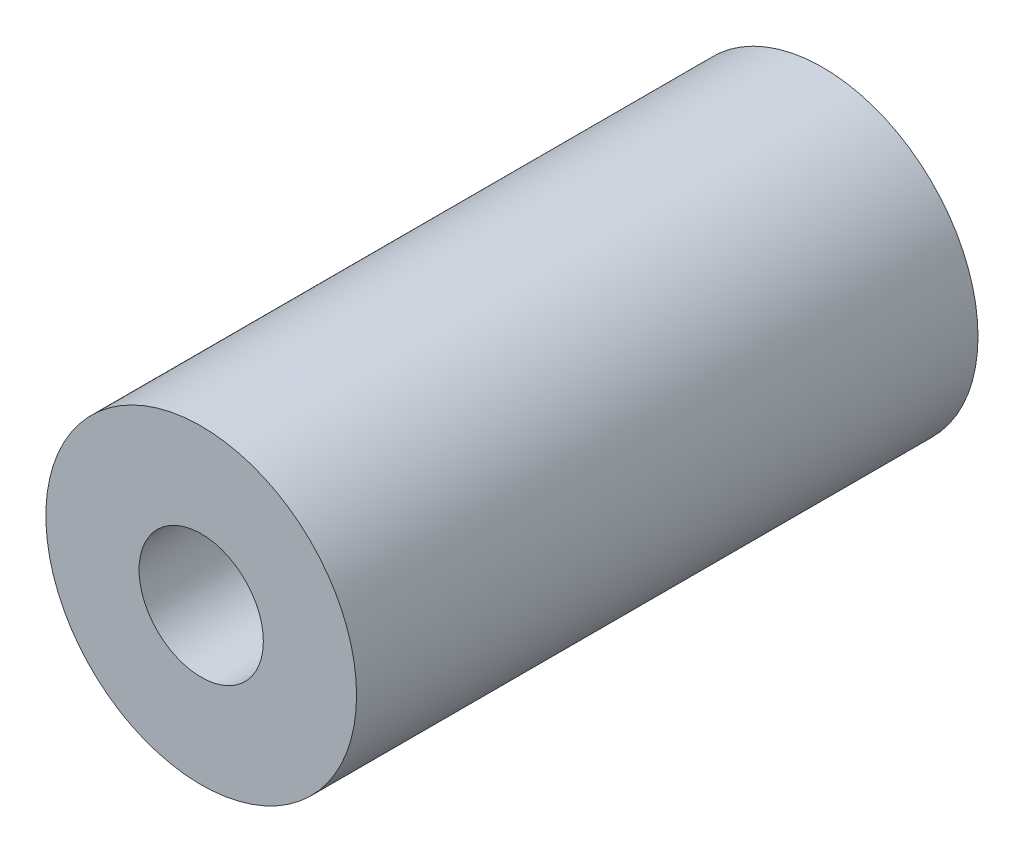
SolidWorks part; units mm, degrees
material "Custom Plastic"
ref_plane "X-Y Datum" through (0, 0, 0) normal (0, 0, 1) x (1, 0, 0)
ref_plane "X-Z Datum" through (0, 0, 0) normal (0, 1, 0) x (1, 0, 0)
ref_plane "Y-Z Datum" through (0, 0, 0) normal (1, 0, 0) x (0, 0, -1)
sketch "Base Sketch" plane through (0, 0, 0) normal (0, 0, 1) x (1, 0, 0)
  circle A0 centre (0, 0) radius 2.5
  circle A1 centre (0, 0) radius 1
  dimension "D1" = 5
  dimension "D2" = 2
extrude "Extrude Pin Body" add sketch "Base Sketch" along normal blind 10 contours A0 A1
